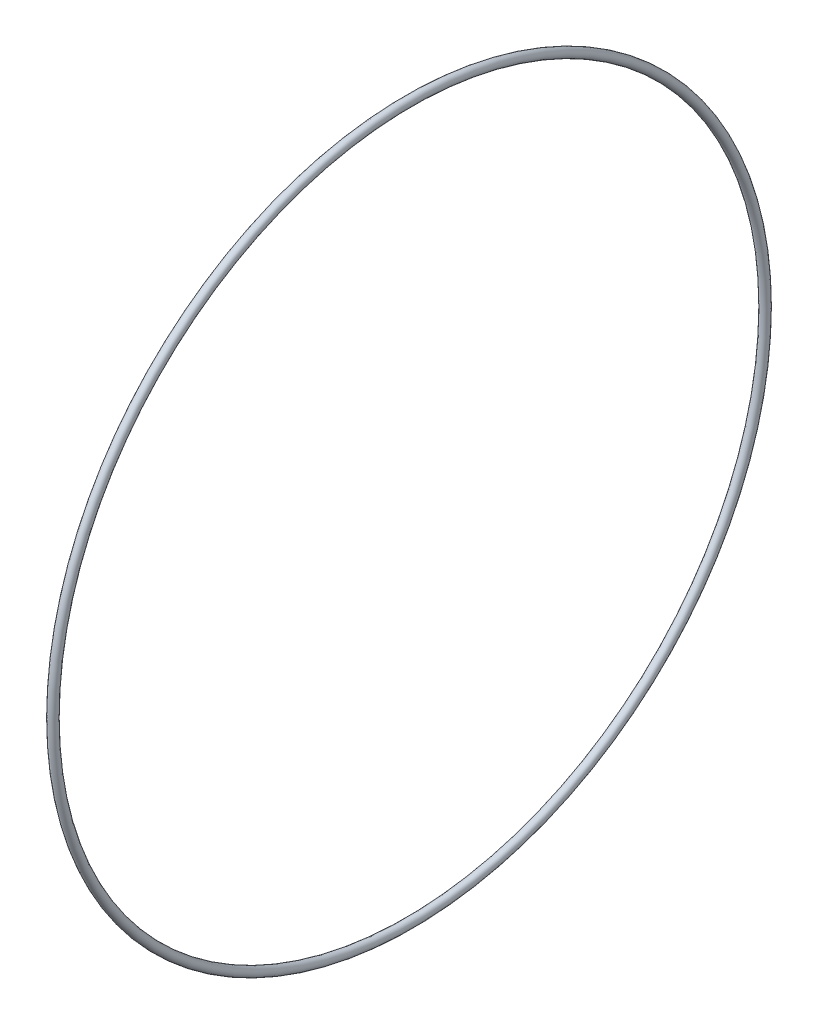
SolidWorks part; units mm, degrees
ref_plane "前视基准面" through (0, 0, 0) normal (0, 0, 1) x (1, 0, 0)
ref_plane "上视基准面" through (0, 0, 0) normal (0, 1, 0) x (1, 0, 0)
ref_plane "右视基准面" through (0, 0, 0) normal (1, 0, 0) x (0, 0, -1)
sketch "草图1" plane through (0, 0, 0) normal (1, 0, 0) x (0, 0, -1)
  circle A0 centre (0, 0) radius 200
  dimension "D1" = 400
sweep "扫描1" add path "草图1" circular profile diameter 5 parameters "D3"=5
